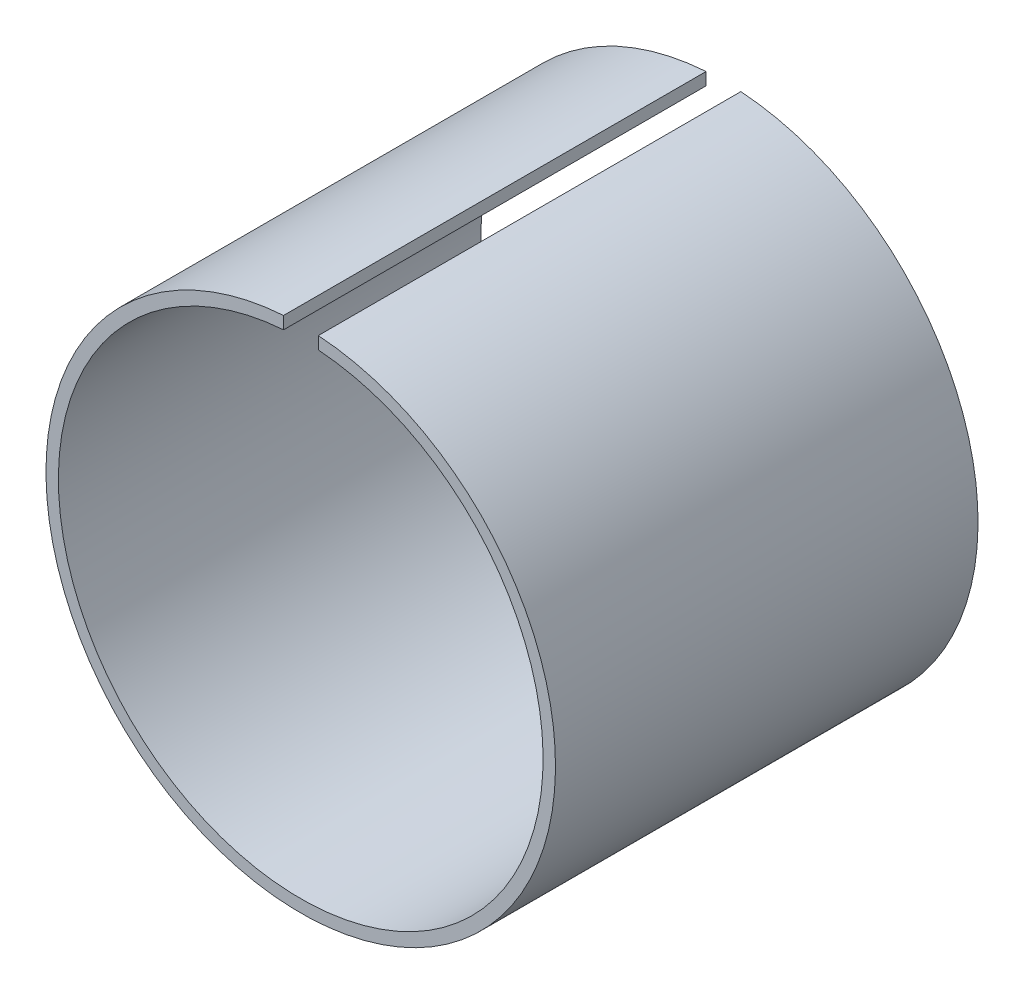
SolidWorks part; units mm, degrees
ref_plane "Front Plane" through (0, 0, 0) normal (0, 0, 1) x (1, 0, 0)
ref_plane "Top Plane" through (0, 0, 0) normal (0, 1, 0) x (1, 0, 0)
ref_plane "Right Plane" through (0, 0, 0) normal (1, 0, 0) x (0, 0, -1)
sketch "Sketch1" plane through (0, 0, 0) normal (0, 0, 1) x (1, 0, 0)
  circle A0 centre (0, 0) radius 19.5
  circle A1 centre (0, 0) radius 20.5
  dimension "D1" = 39
  dimension "D2" = 1
extrude "Boss-Extrude1" add sketch "Sketch1" along normal blind 34
sketch "Sketch2" plane through (0, 0, 34) normal (0, 0, 1) x (1, 0, 0)
  line L1 (-1.3836, 20.9144) -> (1.4144, 20.9144)
  line L2 (-1.3836, 20.9144) -> (-1.3836, 19.2154)
  line L3 (-1.3836, 19.2154) -> (1.4144, 19.2154)
  line L4 (1.4144, 20.9144) -> (1.4144, 19.2154)
extrude "Cut-Extrude1" cut sketch "Sketch2" against normal through all
